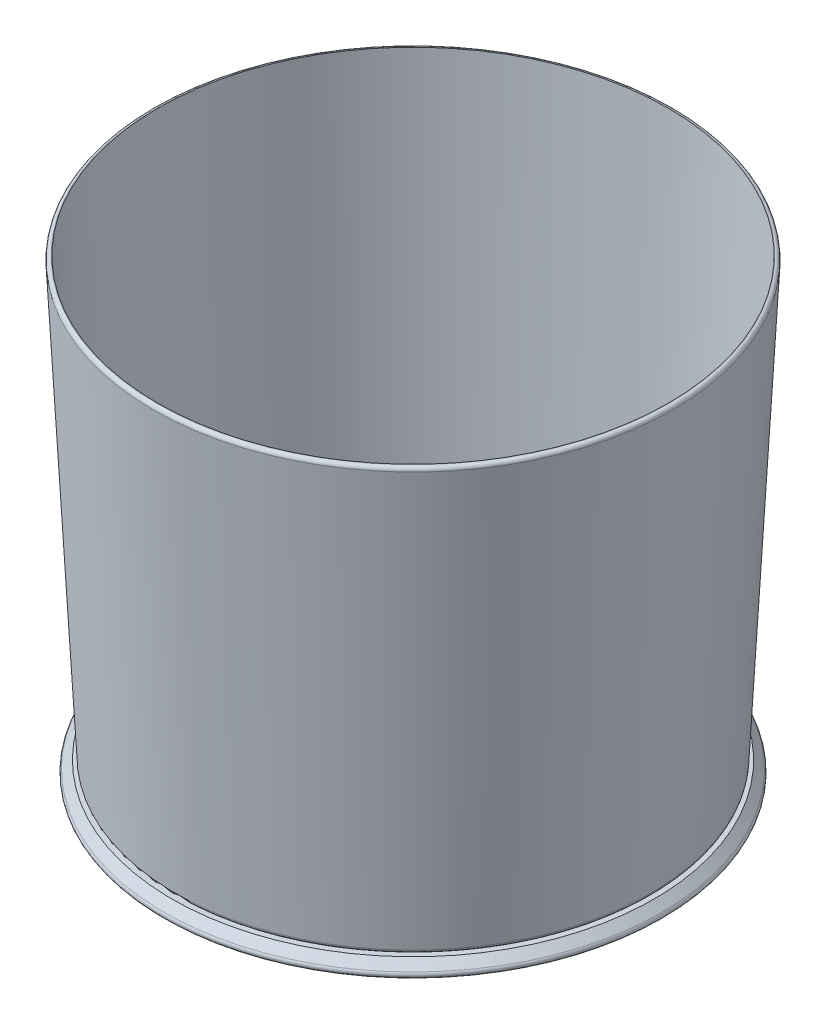
SolidWorks part; units mm, degrees
ref_plane "Front Plane" through (0, 0, 0) normal (0, 0, 1) x (1, 0, 0)
ref_plane "Top Plane" through (0, 0, 0) normal (0, 1, 0) x (1, 0, 0)
ref_plane "Right Plane" through (0, 0, 0) normal (1, 0, 0) x (0, 0, -1)
sketch "Sketch1" plane through (0, 0, 0) normal (0, 0, 1) x (1, 0, 0)
  line L1 (180.8623, -468.3833) -> (171.3604, -468.3833)
  line L2 (176.3539, -463.6386) -> (206.5164, 126.3614)
  line L3 (201.5229, 131.6167) -> (200.8605, 131.6167)
  line L8 (-149.1395, -457.5358) -> (165.9904, -457.5358)
  line L9 (170.9839, -452.7911) -> (200.8605, 131.6167)
  line L10 (180.8623, -468.3833) -> (191.4792, -479.0003)
  line L11 (187.9437, -487.5358) -> (-149.1395, -487.5358)
  line L12 (-150.0083, -212.8371) -> (-150.0083, -325.3793) construction
  line L13 (-149.1395, -487.5358) -> (-149.1395, -457.5358)
  arc A0 (191.4792, -479.0003) -> (187.9437, -487.5358) centre (187.9437, -482.5358) cw
  arc A1 (206.5164, 126.3614) -> (201.5229, 131.6167) centre (201.5229, 126.6167) ccw
  arc A2 (165.9904, -457.5358) -> (170.9839, -452.7911) centre (165.9904, -452.5358) ccw
  arc A3 (171.3604, -468.3833) -> (176.3539, -463.6386) centre (171.3604, -463.3833) ccw
  point P19 (176.1113, -468.3833)
  dimension "D5" = 5
  dimension "D6" = 5
  dimension "D1" = 600
  dimension "D2" = 30
  dimension "D4" = 350
revolve "Revolve1" add sketch "Sketch1" angle 360 about L12
